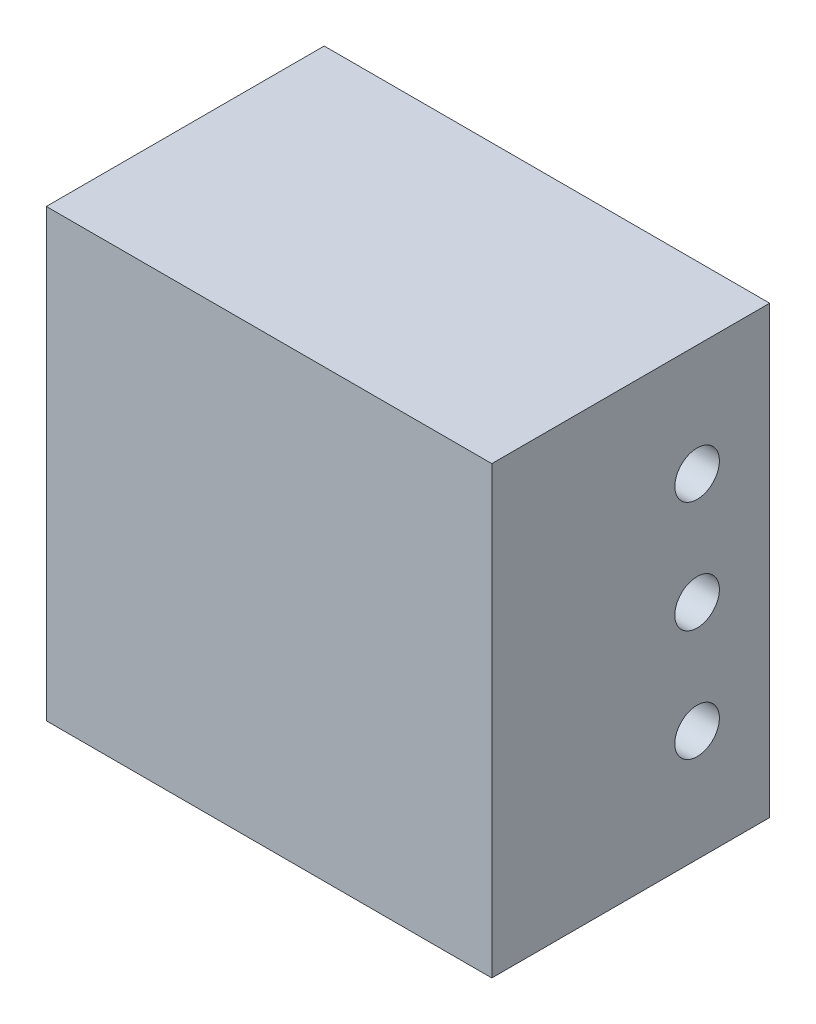
SolidWorks part; units mm, degrees
ref_plane "Front Plane" through (0, 0, 0) normal (0, 0, 1) x (1, 0, 0)
ref_plane "Top Plane" through (0, 0, 0) normal (0, 1, 0) x (1, 0, 0)
ref_plane "Right Plane" through (0, 0, 0) normal (1, 0, 0) x (0, 0, -1)
sketch "Sketch1" plane through (0, 0, 0) normal (1, 0, 0) x (0, 0, -1)
  line L1 (-41.375, 63.5) -> (41.375, 63.5)
  line L2 (-41.375, 63.5) -> (-41.375, -63.5)
  line L3 (-41.375, -63.5) -> (41.375, -63.5)
  line L4 (41.375, 63.5) -> (41.375, -63.5)
  line L5 (-41.375, 63.5) -> (41.375, -63.5) construction
  line L6 (-41.375, -63.5) -> (41.375, 63.5) construction
  point P0 (0, 0)
  dimension "D1" = 127
  dimension "D2" = 82.75
extrude "Boss-Extrude1" add sketch "Sketch1" along normal blind 127
sketch "Sketch2" plane through (127, 0, 0) normal (1, 0, 0) x (0, 0, -1)
  line L0 (41.375, 63.5) -> (0, 63.5)
  line L1 (41.375, 63.5) -> (-41.375, 63.5) construction
  line L2 (20.6875, 63.5) -> (20.6875, -63.5)
  line L3 (-41.375, -63.5) -> (41.375, -63.5) construction
  line L4 (20.6875, 63.5) -> (20.6875, 0)
  line L5 (20.6875, 0) -> (20.6875, -63.5)
  circle A0 centre (20.6875, 31.75) radius 6.35
  circle A1 centre (20.6875, -31.75) radius 6.35
  circle A2 centre (20.6875, 0) radius 6.35
  dimension "D1" = 12.7
  dimension "D2" = 12.7
  dimension "D3" = 12.7
extrude "Cut-Extrude1" cut sketch "Sketch2" against normal blind 127 and the other way through all contours A2 | A0 | A1
sketch "Sketch3" plane through (127, 0, 0) normal (1, 0, 0) x (0, 0, -1)
  line L1 (41.375, 63.5) -> (-41.375, 63.5) construction
  line L3 (-38.635, 63.5) -> (-67.388, 63.5)
  line L4 (-38.635, 63.5) -> (-38.635, -66.1896)
  line L5 (-38.635, -66.1896) -> (-67.388, -66.1896)
  line L6 (-67.388, 63.5) -> (-67.388, -66.1896)
extrude "Cut-Extrude2" cut sketch "Sketch3" against normal blind 127
sketch "Sketch6" plane through (127, 0, 0) normal (1, 0, 0) x (0, 0, -1)
  line L0 (-38.635, 63.5) -> (-37.845, 63.5)
  line L1 (41.375, 63.5) -> (-38.635, 63.5) construction
  line L3 (-37.845, 63.5) -> (-41.0551, 63.5)
  line L4 (-37.845, 63.5) -> (-37.845, -136.5)
  line L5 (-37.845, -136.5) -> (-41.0551, -136.5)
  line L6 (-41.0551, 63.5) -> (-41.0551, -136.5)
  dimension "D1" = 0.79
  dimension "D2" = 200
extrude "Cut-Extrude3" cut sketch "Sketch6" against normal through all contours L3 L6 L5 L4
